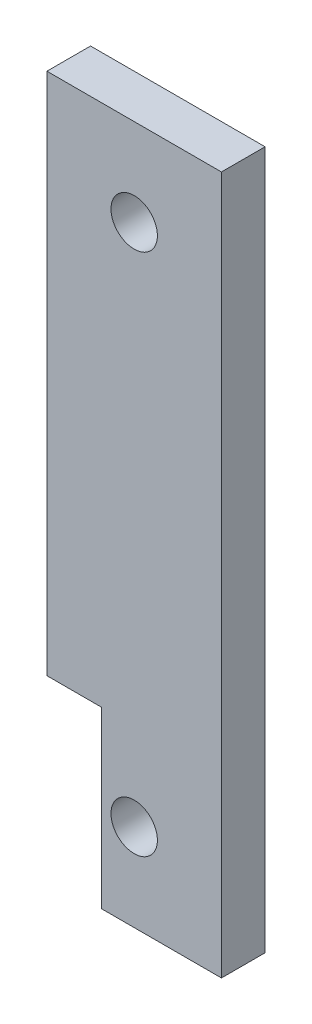
SolidWorks part; units mm, degrees
material "6061-T6 (SS)"
ref_plane "Front Plane" through (0, 0, 0) normal (0, 0, 1) x (1, 0, 0)
ref_plane "Top Plane" through (0, 0, 0) normal (0, 1, 0) x (1, 0, 0)
ref_plane "Right Plane" through (0, 0, 0) normal (1, 0, 0) x (0, 0, -1)
sketch "Sketch1" plane through (0, 0, 0) normal (0, 1, 0) x (1, 0, 0)
  line L1 (0, 0) -> (25.4, 0)
  line L2 (0, 0) -> (0, 6.35)
  line L3 (0, 6.35) -> (25.4, 6.35)
  line L4 (25.4, 0) -> (25.4, 6.35)
  dimension "D1" = 6.35
  dimension "D2" = 25.4
extrude "Boss-Extrude1" add sketch "Sketch1" along normal blind 101.6
hole_wizard "H (0.266) Diameter Hole1" positions "Sketch2" profile "Sketch3" hole size "H" standard "ANSI Inch" end condition up to next
sketch "Sketch2" plane through (0, 0, 0) normal (0, 0, 1) x (1, 0, 0)
  line L0 (0, 101.6) -> (25.4, 101.6) construction
  line L1 (0, 0) -> (25.4, 0) construction
  point P0 (12.7, 88.9)
  point P2 (12.7, 12.7)
  point P7 (12.7, 0)
  dimension "D1" = 12.7
  dimension "D2" = 12.7
sketch "Sketch3" plane through (12.7, 88.9, 0) normal (1, 0, 0) x (0, -1, 0)
  line L0 (0, 0) -> (0, 6.35)
  line L1 (0, 6.35) -> (3.3782, 6.35)
  line L2 (3.3782, 6.35) -> (3.3782, 0)
  line L5 (3.3782, 0) -> (0, 0)
  line L11 (0, -6.35) -> (0, 107.95) construction
  dimension "Thru Hole Dia." = 6.7564
  dimension "Thru Hole Depth" = 6.35
sketch "Sketch4" plane through (0, 0, -6.35) normal (0, 0, -1) x (-1, 0, 0)
  line L1 (0, 0) -> (-7.9375, 0)
  line L2 (0, 0) -> (0, 25.4)
  line L3 (0, 25.4) -> (-7.9375, 25.4)
  line L4 (-7.9375, 0) -> (-7.9375, 25.4)
  circle A0 centre (-12.7, 12.7) radius 3.3782 construction
  dimension "D1" = 12.7
  dimension "D2" = 7.9375
extrude "Cut-Extrude1" cut sketch "Sketch4" against normal through all
